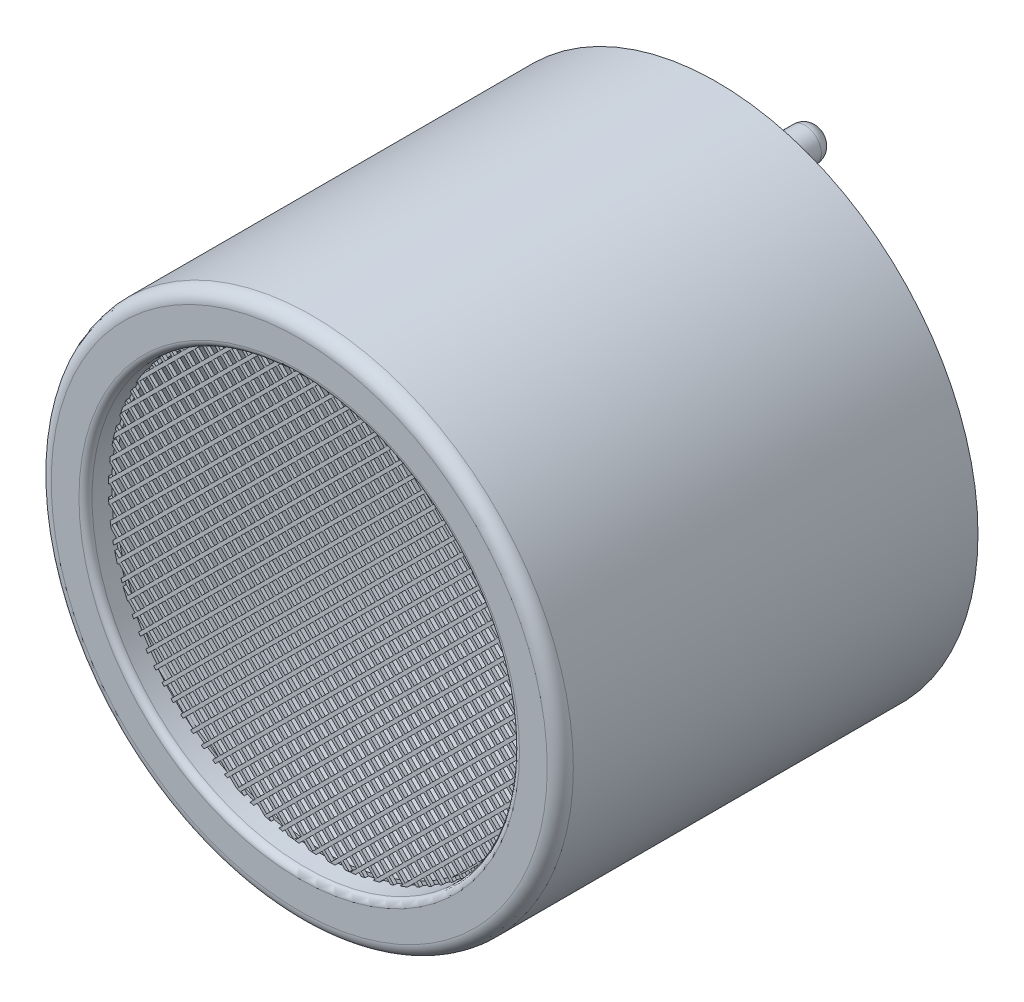
SolidWorks part; units mm, degrees
ref_plane "Plan de face" through (0, 0, 0) normal (0, 0, 1) x (1, 0, 0)
ref_plane "Plan de dessus" through (0, 0, 0) normal (0, 1, 0) x (1, 0, 0)
ref_plane "Plan de droite" through (0, 0, 0) normal (1, 0, 0) x (0, 0, -1)
sketch "Esquisse1" plane through (0, 0, 0) normal (0, 0, 1) x (1, 0, 0)
  circle A0 centre (0, 0) radius 8
  dimension "D1" = 16
extrude "Boss.-Extru.1" add sketch "Esquisse1" against normal blind 12.8
sketch "Esquisse2" plane through (0, 0, 0) normal (0, 0, 1) x (1, 0, 0)
  circle A0 centre (0, 0) radius 6.45
  dimension "D1" = 12.9
extrude "Enlèv. mat.-Extru.1" cut sketch "Esquisse2" against normal blind 10
sketch "Esquisse3" plane through (0, 0, 0) normal (0, 1, 0) x (1, 0, 0)
  line L0 (3.75, 10) -> (3.75, 7.5)
  line L1 (-6.45, 10) -> (6.45, 10) construction
  line L3 (0, 8) -> (0, 10)
  line L4 (0, 10) -> (3.75, 10)
  line L5 (3.75, 7.5) -> (3.25, 7.5)
  line L6 (3.25, 7.5) -> (0, 8)
  dimension "D1" = 3.75
  dimension "D2" = 2.5
  dimension "D3" = 2
  dimension "D4" = 0.5
revolve "Révolution1" add sketch "Esquisse3" angle 360 about L3
sketch "Esquisse4" plane through (0, 0, -10) normal (0, 0, 1) x (1, 0, 0)
  arc A0 (-3.558, 1.1845) -> (-3.558, -1.1845) centre (-3.75, 0) ccw
  circle A1 centre (0, 0) radius 3.75 construction
  circle A2 centre (0, 0) radius 3.75 construction
  arc A3 (-3.558, 1.1845) -> (-3.558, -1.1845) centre (0, 0) ccw
  dimension "D1" = 1.2
extrude "Enlèv. mat.-Extru.2" cut sketch "Esquisse4" against normal through all
sketch "Esquisse5" plane through (0, 0, -12.8) normal (0, 0, -1) x (-1, 0, 0)
  circle A0 centre (0, 5) radius 0.5
  circle A1 centre (0, -5) radius 0.5
  dimension "D1" = 1
  dimension "D2" = 5
  dimension "D3" = 5
extrude "Boss.-Extru.2" add sketch "Esquisse5" along normal blind 1.5
sketch "Esquisse6" plane through (0, 0, -14.3) normal (0, 0, -1) x (-1, 0, 0)
  circle A0 centre (0, 5) radius 1
  circle A1 centre (0, -5) radius 1
  dimension "D1" = 2
extrude "Boss.-Extru.3" add sketch "Esquisse6" along normal blind 0.1
sketch "Esquisse7" plane through (0, 0, -14.4) normal (0, 0, -1) x (-1, 0, 0)
  circle A0 centre (0, 5) radius 0.5
  circle A1 centre (0, -5) radius 0.5
extrude "Boss.-Extru.4" add sketch "Esquisse7" along normal blind 1.5
fillet "Congé1" radius 0.4 4 edges at (-0.5, -5, -15.9) (-0.5, 5, -15.9) (-0.5, -5, -14.4) (-0.5, 5, -14.4)
sketch "Esquisse8" plane through (0, 0, 0) normal (0, 0, 1) x (1, 0, 0)
  circle A0 centre (0, 0) radius 6.55
  circle A1 centre (0, 0) radius 6.45 construction
  dimension "D1" = 0.1
extrude "Enlèv. mat.-Extru.3" cut sketch "Esquisse8" against normal blind 0.8
sketch "Esquisse9" plane through (0, 0, -0.8) normal (0, 0, 1) x (1, 0, 0)
  line L0 (0, 0) -> (3.25, 0) construction
  line L1 (-4.6315, -4.6315) -> (4.6315, 4.6315)
  line L2 (-4.5603, -4.7017) -> (4.7017, 4.5603)
  line L3 (4.6315, 4.6315) -> (4.7017, 4.5603)
  line L4 (-4.6315, -4.6315) -> (-4.5603, -4.7017)
  line L5 (-4.3401, -4.9057) -> (4.9057, 4.3401)
  line L6 (4.9057, 4.3401) -> (4.9716, 4.2645)
  line L7 (4.9716, 4.2645) -> (-4.2645, -4.9716)
  line L8 (-4.2645, -4.9716) -> (-4.3401, -4.9057)
  line L9 (-4.0312, -5.1626) -> (5.1626, 4.0312)
  line L10 (5.1626, 4.0312) -> (5.224, 3.9512)
  line L11 (5.224, 3.9512) -> (-3.9512, -5.224)
  line L12 (-3.9512, -5.224) -> (-4.0312, -5.1626)
  line L13 (-3.7046, -5.4017) -> (5.4017, 3.7046)
  line L14 (5.4017, 3.7046) -> (5.4586, 3.6202)
  line L15 (5.4586, 3.6202) -> (-3.6202, -5.4586)
  line L16 (-3.6202, -5.4586) -> (-3.7046, -5.4017)
  line L21 (-3.3599, -5.6226) -> (5.6226, 3.3599)
  line L22 (5.6226, 3.3599) -> (5.6749, 3.2708)
  line L23 (5.6749, 3.2708) -> (-3.2708, -5.6749)
  line L24 (-3.2708, -5.6749) -> (-3.3599, -5.6226)
  line L25 (-2.9961, -5.8246) -> (5.8246, 2.9961)
  line L26 (5.8246, 2.9961) -> (5.872, 2.9021)
  line L27 (5.872, 2.9021) -> (-2.9021, -5.872)
  line L28 (-2.9021, -5.872) -> (-2.9961, -5.8246)
  line L29 (-2.6124, -6.0065) -> (6.0065, 2.6124)
  line L30 (6.0065, 2.6124) -> (6.0487, 2.5132)
  line L31 (6.0487, 2.5132) -> (-2.5132, -6.0487)
  line L32 (-2.5132, -6.0487) -> (-2.6124, -6.0065)
  line L33 (-2.2071, -6.1669) -> (6.1669, 2.2071)
  line L34 (6.1669, 2.2071) -> (6.2035, 2.1023)
  line L35 (6.2035, 2.1023) -> (-2.1023, -6.2035)
  line L36 (-2.1023, -6.2035) -> (-2.2071, -6.1669)
  line L37 (-1.7785, -6.3039) -> (6.3039, 1.7785)
  line L38 (6.3039, 1.7785) -> (6.3342, 1.6673)
  line L39 (6.3342, 1.6673) -> (-1.6673, -6.3342)
  line L40 (-1.6673, -6.3342) -> (-1.7785, -6.3039)
  line L41 (-1.3237, -6.4149) -> (6.4149, 1.3237)
  line L42 (6.4149, 1.3237) -> (6.4381, 1.2055)
  line L43 (6.4381, 1.2055) -> (-1.2055, -6.4381)
  line L44 (-1.2055, -6.4381) -> (-1.3237, -6.4149)
  line L45 (-0.8392, -6.496) -> (6.496, 0.8392)
  line L46 (6.496, 0.8392) -> (6.5111, 0.7128)
  line L47 (6.5111, 0.7128) -> (-0.7128, -6.5111)
  line L48 (-0.7128, -6.5111) -> (-0.8392, -6.496)
  line L49 (-0.3197, -6.5422) -> (6.5422, 0.3197)
  line L50 (6.5422, 0.3197) -> (6.5474, 0.1835)
  line L51 (6.5474, 0.1835) -> (-0.1835, -6.5474)
  line L52 (-0.1835, -6.5474) -> (-0.3197, -6.5422)
  line L53 (0.2427, -6.5455) -> (6.5455, -0.2427)
  line L54 (6.5455, -0.2427) -> (6.5383, -0.3913)
  line L55 (6.5383, -0.3913) -> (0.3913, -6.5383)
  line L56 (0.3913, -6.5383) -> (0.2427, -6.5455)
  line L57 (0.8607, -6.4932) -> (6.4932, -0.8607)
  line L58 (6.4932, -0.8607) -> (6.4691, -1.0262)
  line L59 (6.4691, -1.0262) -> (1.0262, -6.4691)
  line L60 (1.0262, -6.4691) -> (0.8607, -6.4932)
  line L61 (1.5574, -6.3621) -> (6.3621, -1.5574)
  line L62 (6.3621, -1.5574) -> (6.3122, -1.7488)
  line L63 (6.3122, -1.7488) -> (1.7488, -6.3122)
  line L64 (1.7488, -6.3122) -> (1.5574, -6.3621)
  line L65 (2.3849, -6.1004) -> (6.1004, -2.3849)
  line L66 (6.1004, -2.3849) -> (6.0004, -2.6263)
  line L67 (6.0004, -2.6263) -> (2.6263, -6.0004)
  line L68 (2.6263, -6.0004) -> (2.3849, -6.1004)
  line L69 (3.9587, -5.0923) -> (5.0923, -3.9587)
  line L73 (-4.8388, -4.4146) -> (4.4146, 4.8388)
  line L74 (4.4146, 4.8388) -> (4.3401, 4.9057)
  line L75 (4.3401, 4.9057) -> (-4.9057, -4.3401)
  line L76 (-4.9057, -4.3401) -> (-4.8388, -4.4146)
  line L77 (-5.1, -4.11) -> (4.11, 5.1)
  line L78 (4.11, 5.1) -> (4.0312, 5.1626)
  line L79 (4.0312, 5.1626) -> (-5.1626, -4.0312)
  line L80 (-5.1626, -4.0312) -> (-5.1, -4.11)
  line L81 (-5.3436, -3.788) -> (3.788, 5.3436)
  line L82 (3.788, 5.3436) -> (3.7046, 5.4017)
  line L83 (3.7046, 5.4017) -> (-5.4017, -3.7046)
  line L84 (-5.4017, -3.7046) -> (-5.3436, -3.788)
  line L85 (-5.5691, -3.4478) -> (3.4478, 5.5691)
  line L86 (3.4478, 5.5691) -> (3.3599, 5.6226)
  line L87 (3.3599, 5.6226) -> (-5.6226, -3.3599)
  line L88 (-5.6226, -3.3599) -> (-5.5691, -3.4478)
  line L89 (-5.7759, -3.0889) -> (3.0889, 5.7759)
  line L90 (3.0889, 5.7759) -> (2.9961, 5.8246)
  line L91 (2.9961, 5.8246) -> (-5.8246, -2.9961)
  line L92 (-5.8246, -2.9961) -> (-5.7759, -3.0889)
  line L93 (-5.963, -2.7103) -> (2.7103, 5.963)
  line L94 (2.7103, 5.963) -> (2.6124, 6.0065)
  line L95 (2.6124, 6.0065) -> (-6.0065, -2.6124)
  line L96 (-6.0065, -2.6124) -> (-5.963, -2.7103)
  line L97 (-6.1289, -2.3106) -> (2.3106, 6.1289)
  line L98 (2.3106, 6.1289) -> (2.2071, 6.1669)
  line L99 (2.2071, 6.1669) -> (-6.1669, -2.2071)
  line L100 (-6.1669, -2.2071) -> (-6.1289, -2.3106)
  line L101 (-6.272, -1.888) -> (1.888, 6.272)
  line L102 (1.888, 6.272) -> (1.7785, 6.3039)
  line L103 (1.7785, 6.3039) -> (-6.3039, -1.7785)
  line L104 (-6.3039, -1.7785) -> (-6.272, -1.888)
  line L105 (-6.3897, -1.44) -> (1.44, 6.3897)
  line L106 (1.44, 6.3897) -> (1.3237, 6.4149)
  line L107 (1.3237, 6.4149) -> (-6.4149, -1.3237)
  line L108 (-6.4149, -1.3237) -> (-6.3897, -1.44)
  line L109 (-6.4788, -0.9633) -> (0.9633, 6.4788)
  line L110 (0.9633, 6.4788) -> (0.8392, 6.496)
  line L111 (0.8392, 6.496) -> (-6.496, -0.8392)
  line L112 (-6.496, -0.8392) -> (-6.4788, -0.9633)
  line L113 (-6.5343, -0.4532) -> (0.4532, 6.5343)
  line L114 (0.4532, 6.5343) -> (0.3197, 6.5422)
  line L115 (0.3197, 6.5422) -> (-6.5422, -0.3197)
  line L116 (-6.5422, -0.3197) -> (-6.5343, -0.4532)
  line L117 (-6.5493, 0.0975) -> (-0.0975, 6.5493)
  line L118 (-0.0975, 6.5493) -> (-0.2427, 6.5455)
  line L119 (-0.2427, 6.5455) -> (-6.5455, 0.2427)
  line L120 (-6.5455, 0.2427) -> (-6.5493, 0.0975)
  line L121 (-6.5125, 0.7) -> (-0.7, 6.5125)
  line L122 (-0.7, 6.5125) -> (-0.8607, 6.4932)
  line L123 (-0.8607, 6.4932) -> (-6.4932, 0.8607)
  line L124 (-6.4932, 0.8607) -> (-6.5125, 0.7)
  line L125 (-6.4043, 1.3739) -> (-1.3739, 6.4043)
  line L126 (-1.3739, 6.4043) -> (-1.5575, 6.3621)
  line L127 (-1.5575, 6.3621) -> (-6.3621, 1.5575)
  line L128 (-6.3621, 1.5575) -> (-6.4043, 1.3739)
  line L129 (-6.1835, 2.1604) -> (-2.1604, 6.1835)
  line L130 (-2.1604, 6.1835) -> (-2.3849, 6.1004)
  line L132 (-6.1004, 2.3849) -> (-6.1835, 2.1604)
  line L133 (-6.1004, 2.3849) -> (-2.3849, 6.1004)
  line L135 (-3.1874, 5.7222) -> (-5.7222, 3.1874)
  line L137 (-5.511, 3.54) -> (-3.54, 5.511)
  line L138 (-3.54, 5.511) -> (-3.1874, 5.7222)
  line L139 (-5.7222, 3.1874) -> (-5.511, 3.54)
  circle A0 centre (0, 0) radius 3.25 construction
  circle A1 centre (0, 0) radius 6.55 construction
  circle A2 centre (0, 0) radius 6.55 construction
  circle A4 centre (0, 0) radius 6.45 construction
  arc A5 (5.0923, -3.9587) -> (3.9587, -5.0923) centre (0, 0) cw
  dimension "D4" = 0.1
  dimension "D33" = 0.3
  dimension "D1" = 45
  dimension "D2" = 0.1
  dimension "D3" = 0.3
  dimension "D5" = 0.3
  dimension "D6" = 0.1
  dimension "D7" = 0.3
  dimension "D8" = 0.1
  dimension "D9" = 0.3
  dimension "D10" = 0.1
  dimension "D11" = 0.3
  dimension "D12" = 0.1
  dimension "D13" = 0.3
  dimension "D14" = 0.1
  dimension "D15" = 0.3
  dimension "D16" = 0.1
  dimension "D17" = 0.3
  dimension "D18" = 0.1
  dimension "D19" = 0.3
  dimension "D20" = 0.1
  dimension "D21" = 0.3
  dimension "D22" = 0.1
  dimension "D23" = 0.3
  dimension "D24" = 0.1
  dimension "D25" = 0.3
  dimension "D26" = 0.1
  dimension "D27" = 0.3
  dimension "D28" = 0.1
  dimension "D29" = 0.3
  dimension "D30" = 0.1
  dimension "D31" = 0.1
  dimension "D32" = 0.3
  dimension "D34" = 0.3
  dimension "D35" = 0.1
  dimension "D36" = 0.3
  dimension "D37" = 0.1
  dimension "D38" = 0.3
  dimension "D39" = 0.1
  dimension "D40" = 0.3
  dimension "D41" = 0.1
  dimension "D42" = 0.3
  dimension "D43" = 0.1
  dimension "D44" = 0.3
  dimension "D45" = 0.1
  dimension "D46" = 0.3
  dimension "D47" = 0.1
  dimension "D48" = 0.3
  dimension "D49" = 0.1
  dimension "D50" = 0.3
  dimension "D51" = 0.1
  dimension "D52" = 0.3
  dimension "D53" = 0.1
  dimension "D54" = 0.3
  dimension "D55" = 0.1
  dimension "D56" = 0.3
  dimension "D57" = 0.1
  dimension "D58" = 0.3
  dimension "D59" = 0.1
  dimension "D60" = 0.3
  dimension "D61" = 0.1
  dimension "D62" = 0.3
  dimension "D63" = 0.1
  dimension "D64" = 0.1
  dimension "D65" = 0.3
extrude "Boss.-Extru.5" add sketch "Esquisse9" along normal blind 0.1 separate body
sketch "Esquisse11" plane through (0, 0, -0.8) normal (0, 0, -1) x (-1, 0, 0)
  line L0 (0, 0) -> (-5.6875, 0) construction
  line L1 (-4.6315, -4.6315) -> (4.6315, 4.6315)
  line L2 (-4.5603, -4.7017) -> (4.7017, 4.5603)
  line L3 (4.6315, 4.6315) -> (4.7017, 4.5603)
  line L4 (-4.6315, -4.6315) -> (-4.5603, -4.7017)
  line L5 (-4.3401, -4.9057) -> (4.9057, 4.3401)
  line L6 (4.9057, 4.3401) -> (4.9716, 4.2645)
  line L7 (4.9716, 4.2645) -> (-4.2645, -4.9716)
  line L8 (-4.2645, -4.9716) -> (-4.3401, -4.9057)
  line L9 (-4.0312, -5.1626) -> (5.1626, 4.0312)
  line L10 (5.1626, 4.0312) -> (5.224, 3.9512)
  line L11 (5.224, 3.9512) -> (-3.9512, -5.224)
  line L12 (-3.9512, -5.224) -> (-4.0312, -5.1626)
  line L13 (-3.7046, -5.4017) -> (5.4017, 3.7046)
  line L14 (5.4017, 3.7046) -> (5.4586, 3.6202)
  line L15 (5.4586, 3.6202) -> (-3.6202, -5.4586)
  line L16 (-3.6202, -5.4586) -> (-3.7046, -5.4017)
  line L17 (-3.3599, -5.6226) -> (5.6226, 3.3599)
  line L18 (5.6226, 3.3599) -> (5.6749, 3.2708)
  line L19 (5.6749, 3.2708) -> (-3.2708, -5.6749)
  line L20 (-3.2708, -5.6749) -> (-3.3599, -5.6226)
  line L21 (-2.9961, -5.8246) -> (5.8246, 2.9961)
  line L22 (5.8246, 2.9961) -> (5.872, 2.9021)
  line L23 (5.872, 2.9021) -> (-2.9021, -5.872)
  line L24 (-2.9021, -5.872) -> (-2.9961, -5.8246)
  line L25 (-2.6124, -6.0065) -> (6.0065, 2.6124)
  line L26 (6.0065, 2.6124) -> (6.0487, 2.5132)
  line L27 (6.0487, 2.5132) -> (-2.5132, -6.0487)
  line L28 (-2.5132, -6.0487) -> (-2.6124, -6.0065)
  line L29 (-2.2071, -6.1669) -> (6.1669, 2.2071)
  line L30 (6.1669, 2.2071) -> (6.2035, 2.1023)
  line L31 (6.2035, 2.1023) -> (-2.1023, -6.2035)
  line L32 (-2.1023, -6.2035) -> (-2.2071, -6.1669)
  line L33 (-1.7785, -6.3039) -> (6.3039, 1.7785)
  line L34 (6.3039, 1.7785) -> (6.3342, 1.6673)
  line L35 (6.3342, 1.6673) -> (-1.6673, -6.3342)
  line L36 (-1.6673, -6.3342) -> (-1.7785, -6.3039)
  line L37 (-1.3237, -6.4149) -> (6.4149, 1.3237)
  line L38 (6.4149, 1.3237) -> (6.4381, 1.2055)
  line L39 (6.4381, 1.2055) -> (-1.2055, -6.4381)
  line L40 (-1.2055, -6.4381) -> (-1.3237, -6.4149)
  line L41 (-0.8392, -6.496) -> (6.496, 0.8392)
  line L42 (6.496, 0.8392) -> (6.5111, 0.7128)
  line L43 (6.5111, 0.7128) -> (-0.7128, -6.5111)
  line L44 (-0.7128, -6.5111) -> (-0.8392, -6.496)
  line L45 (-0.3197, -6.5422) -> (6.5422, 0.3197)
  line L46 (6.5422, 0.3197) -> (6.5474, 0.1835)
  line L47 (6.5474, 0.1835) -> (-0.1835, -6.5474)
  line L48 (-0.1835, -6.5474) -> (-0.3197, -6.5422)
  line L49 (0.2427, -6.5455) -> (6.5455, -0.2427)
  line L50 (6.5455, -0.2427) -> (6.5383, -0.3913)
  line L51 (6.5383, -0.3913) -> (0.3913, -6.5383)
  line L52 (0.3913, -6.5383) -> (0.2427, -6.5455)
  line L53 (0.8607, -6.4932) -> (6.4932, -0.8607)
  line L54 (6.4932, -0.8607) -> (6.4691, -1.0262)
  line L55 (6.4691, -1.0262) -> (1.0262, -6.4691)
  line L56 (1.0262, -6.4691) -> (0.8607, -6.4932)
  line L57 (1.5574, -6.3621) -> (6.3621, -1.5574)
  line L58 (6.3621, -1.5574) -> (6.3122, -1.7488)
  line L59 (6.3122, -1.7488) -> (1.7488, -6.3122)
  line L60 (1.7488, -6.3122) -> (1.5574, -6.3621)
  line L61 (2.3849, -6.1004) -> (6.1004, -2.3849)
  line L62 (6.1004, -2.3849) -> (6.0004, -2.6263)
  line L63 (6.0004, -2.6263) -> (2.6263, -6.0004)
  line L64 (2.6263, -6.0004) -> (2.3849, -6.1004)
  line L65 (3.9587, -5.0923) -> (5.0923, -3.9587)
  line L66 (-4.8388, -4.4146) -> (4.4146, 4.8388)
  line L67 (4.4146, 4.8388) -> (4.3401, 4.9057)
  line L68 (4.3401, 4.9057) -> (-4.9057, -4.3401)
  line L69 (-4.9057, -4.3401) -> (-4.8388, -4.4146)
  line L70 (-5.1, -4.11) -> (4.11, 5.1)
  line L71 (4.11, 5.1) -> (4.0312, 5.1626)
  line L72 (4.0312, 5.1626) -> (-5.1626, -4.0312)
  line L73 (-5.1626, -4.0312) -> (-5.1, -4.11)
  line L74 (-5.3436, -3.788) -> (3.788, 5.3436)
  line L75 (3.788, 5.3436) -> (3.7046, 5.4017)
  line L76 (3.7046, 5.4017) -> (-5.4017, -3.7046)
  line L77 (-5.4017, -3.7046) -> (-5.3436, -3.788)
  line L78 (-5.5691, -3.4478) -> (3.4478, 5.5691)
  line L79 (3.4478, 5.5691) -> (3.3599, 5.6226)
  line L80 (3.3599, 5.6226) -> (-5.6226, -3.3599)
  line L81 (-5.6226, -3.3599) -> (-5.5691, -3.4478)
  line L82 (-5.7759, -3.0889) -> (3.0889, 5.7759)
  line L83 (3.0889, 5.7759) -> (2.9961, 5.8246)
  line L84 (2.9961, 5.8246) -> (-5.8246, -2.9961)
  line L85 (-5.8246, -2.9961) -> (-5.7759, -3.0889)
  line L86 (-5.963, -2.7103) -> (2.7103, 5.963)
  line L87 (2.7103, 5.963) -> (2.6124, 6.0065)
  line L88 (2.6124, 6.0065) -> (-6.0065, -2.6124)
  line L89 (-6.0065, -2.6124) -> (-5.963, -2.7103)
  line L90 (-6.1289, -2.3106) -> (2.3106, 6.1289)
  line L91 (2.3106, 6.1289) -> (2.2071, 6.1669)
  line L92 (2.2071, 6.1669) -> (-6.1669, -2.2071)
  line L93 (-6.1669, -2.2071) -> (-6.1289, -2.3106)
  line L94 (-6.272, -1.888) -> (1.888, 6.272)
  line L95 (1.888, 6.272) -> (1.7785, 6.3039)
  line L96 (1.7785, 6.3039) -> (-6.3039, -1.7785)
  line L97 (-6.3039, -1.7785) -> (-6.272, -1.888)
  line L98 (-6.3897, -1.44) -> (1.44, 6.3897)
  line L99 (1.44, 6.3897) -> (1.3237, 6.4149)
  line L100 (1.3237, 6.4149) -> (-6.4149, -1.3237)
  line L101 (-6.4149, -1.3237) -> (-6.3897, -1.44)
  line L102 (-6.4788, -0.9633) -> (0.9633, 6.4788)
  line L103 (0.9633, 6.4788) -> (0.8392, 6.496)
  line L104 (0.8392, 6.496) -> (-6.496, -0.8392)
  line L105 (-6.496, -0.8392) -> (-6.4788, -0.9633)
  line L106 (-6.5343, -0.4532) -> (0.4532, 6.5343)
  line L107 (0.4532, 6.5343) -> (0.3197, 6.5422)
  line L108 (0.3197, 6.5422) -> (-6.5422, -0.3197)
  line L109 (-6.5422, -0.3197) -> (-6.5343, -0.4532)
  line L110 (-6.5493, 0.0975) -> (-0.0975, 6.5493)
  line L111 (-0.0975, 6.5493) -> (-0.2427, 6.5455)
  line L112 (-0.2427, 6.5455) -> (-6.5455, 0.2427)
  line L113 (-6.5455, 0.2427) -> (-6.5493, 0.0975)
  line L114 (-6.5125, 0.7) -> (-0.7, 6.5125)
  line L115 (-0.7, 6.5125) -> (-0.8607, 6.4932)
  line L116 (-0.8607, 6.4932) -> (-6.4932, 0.8607)
  line L117 (-6.4932, 0.8607) -> (-6.5125, 0.7)
  line L118 (-6.4043, 1.3739) -> (-1.3739, 6.4043)
  line L119 (-1.3739, 6.4043) -> (-1.5575, 6.3621)
  line L120 (-1.5575, 6.3621) -> (-6.3621, 1.5575)
  line L121 (-6.3621, 1.5575) -> (-6.4043, 1.3739)
  line L122 (-6.1835, 2.1604) -> (-2.1604, 6.1835)
  line L123 (-2.1604, 6.1835) -> (-2.3849, 6.1004)
  line L124 (-6.1004, 2.3849) -> (-6.1835, 2.1604)
  line L125 (-6.1004, 2.3849) -> (-2.3849, 6.1004)
  line L126 (-3.1874, 5.7222) -> (-5.7222, 3.1874)
  line L127 (-5.511, 3.54) -> (-3.54, 5.511)
  line L128 (-3.54, 5.511) -> (-3.1874, 5.7222)
  line L129 (-5.7222, 3.1874) -> (-5.511, 3.54)
  arc A0 (5.0923, -3.9587) -> (3.9587, -5.0923) centre (0, 0) cw
  dimension "D1" = 45
  dimension "D2" = 0.1
  dimension "D3" = 0.3
  dimension "D4" = 0.1
  dimension "D5" = 0.3
  dimension "D6" = 0.1
  dimension "D7" = 0.3
  dimension "D8" = 0.1
  dimension "D9" = 0.3
  dimension "D10" = 0.1
  dimension "D11" = 0.3
  dimension "D12" = 0.1
  dimension "D13" = 0.3
  dimension "D14" = 0.1
  dimension "D15" = 0.3
  dimension "D16" = 0.1
  dimension "D17" = 0.3
  dimension "D18" = 0.1
  dimension "D19" = 0.3
  dimension "D20" = 0.1
  dimension "D21" = 0.3
  dimension "D22" = 0.1
  dimension "D23" = 0.3
  dimension "D24" = 0.1
  dimension "D25" = 0.3
  dimension "D26" = 0.1
  dimension "D27" = 0.3
  dimension "D28" = 0.1
  dimension "D29" = 0.3
  dimension "D30" = 0.1
  dimension "D31" = 0.1
  dimension "D32" = 0.3
  dimension "D33" = 0.3
  dimension "D34" = 0.3
  dimension "D35" = 0.1
  dimension "D36" = 0.3
  dimension "D37" = 0.1
  dimension "D38" = 0.3
  dimension "D39" = 0.1
  dimension "D40" = 0.3
  dimension "D41" = 0.1
  dimension "D42" = 0.3
  dimension "D43" = 0.1
  dimension "D44" = 0.3
  dimension "D45" = 0.1
  dimension "D46" = 0.3
  dimension "D47" = 0.1
  dimension "D48" = 0.3
  dimension "D49" = 0.1
  dimension "D50" = 0.3
  dimension "D51" = 0.1
  dimension "D52" = 0.3
  dimension "D53" = 0.1
  dimension "D54" = 0.3
  dimension "D55" = 0.1
  dimension "D56" = 0.3
  dimension "D57" = 0.1
  dimension "D58" = 0.3
  dimension "D59" = 0.1
  dimension "D60" = 0.3
  dimension "D61" = 0.1
  dimension "D62" = 0.3
  dimension "D63" = 0.1
  dimension "D64" = 0.1
  dimension "D65" = 0.3
extrude "Boss.-Extru.8" add sketch "Esquisse11" against normal blind 0.1 separate body
fillet "Congé2" radius 0.4 1 edges at (8, 0, 0)
fillet "Congé3" radius 0.2 1 edges at (6.55, 0, 0)
